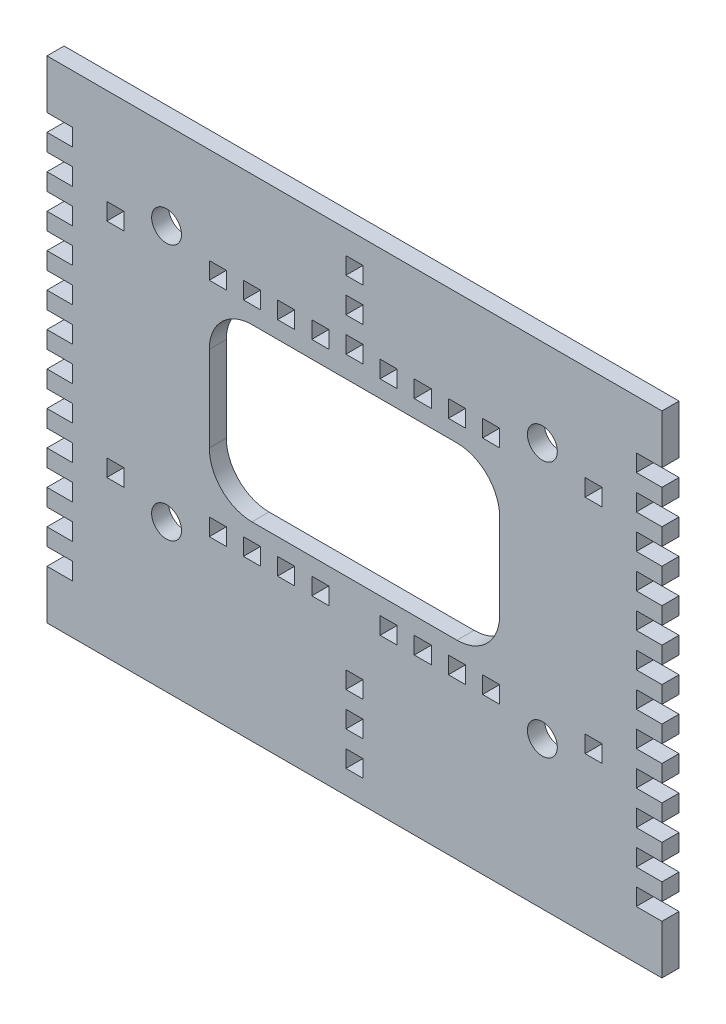
SolidWorks part; units mm, degrees
material "Cedar"
ref_plane "Front Plane" through (0, 0, 0) normal (0, 0, 1) x (1, 0, 0)
ref_plane "Top Plane" through (0, 0, 0) normal (0, 1, 0) x (1, 0, 0)
ref_plane "Right Plane" through (0, 0, 0) normal (1, 0, 0) x (0, 0, -1)
sketch "Sketch1" plane through (0, 0, 0) normal (0, 0, 1) x (1, 0, 0)
  line L0 (0, 0) -> (0, 50) construction
  line L1 (0, 0) -> (-60, 0) construction
  line L2 (-72, -57.5) -> (-72, 57.5)
  line L3 (-72, 57.5) -> (72, 57.5)
  line L6 (-2, 44) -> (2, 44)
  line L7 (72, -57.5) -> (72, 57.5)
  line L8 (-72, -57.5) -> (72, -57.5)
  line L9 (-24, 27) -> (24, 27)
  line L10 (-75.7581, 7) -> (88.9053, 7) construction
  line L11 (-34, 17) -> (-34, -3)
  line L12 (-24, -13) -> (24, -13)
  line L13 (34, 17) -> (34, -3)
  line L14 (-2, 52) -> (2, 52)
  line L15 (-2, 52) -> (-2, 48)
  line L16 (-2, 48) -> (2, 48)
  line L17 (2, 52) -> (2, 48)
  line L18 (-2, 44) -> (-2, 40)
  line L19 (-2, 40) -> (2, 40)
  line L20 (2, 44) -> (2, 40)
  line L21 (-2, 36) -> (2, 36)
  line L22 (-2, 36) -> (-2, 32)
  line L23 (-2, 32) -> (2, 32)
  line L24 (2, 36) -> (2, 32)
  line L25 (2, -36) -> (2, -32)
  line L26 (-2, -32) -> (2, -32)
  line L27 (-2, -36) -> (-2, -32)
  line L28 (-2, -36) -> (2, -36)
  line L29 (2, -44) -> (2, -40)
  line L30 (-2, -40) -> (2, -40)
  line L31 (-2, -44) -> (-2, -40)
  line L32 (2, -52) -> (2, -48)
  line L33 (-2, -48) -> (2, -48)
  line L34 (-2, -52) -> (-2, -48)
  line L35 (-2, -52) -> (2, -52)
  line L36 (-2, -44) -> (2, -44)
  circle A0 centre (-44, 37) radius 3.5
  arc A1 (-34, -3) -> (-24, -13) centre (-24, -3) ccw
  arc A2 (34, -3) -> (24, -13) centre (24, -3) cw
  circle A3 centre (44, 37) radius 3.5
  circle A4 centre (44, -23) radius 3.5
  circle A5 centre (-44, -23) radius 3.5
  arc A6 (34, 17) -> (24, 27) centre (24, 17) ccw
  arc A7 (-24, 27) -> (-34, 17) centre (-24, 17) ccw
  point P21 (0, 57.5)
  point P27 (-72, 0)
  point P28 (72, 0)
  dimension "D3" = 7
  dimension "D8" = 20
  dimension "D10" = 10
  dimension "D1" = 20.5
  dimension "D2" = 28
  dimension "D4" = 44
  dimension "D5" = 34
  dimension "D6" = 34
  dimension "D7" = 20
  dimension "D9" = 30
  dimension "D11" = 5.5
  dimension "D12" = 4
  dimension "D13" = 4
  dimension "D14" = 2
  dimension "D15" = 3
extrude "Boss-Extrude1" add sketch "Sketch1" along normal blind 4
sketch "Sketch2" plane through (0, 0, 4) normal (0, 0, 1) x (1, 0, 0)
  line L0 (0, 0) -> (-89.2695, 0) construction
  line L1 (0, 0) -> (0, 71.1996) construction
  line L2 (-72, -57.5) -> (-72, 57.5) construction
  line L3 (-72, 10) -> (-66, 10)
  line L4 (-72, 10) -> (-72, 14)
  line L5 (-72, 14) -> (-66, 14)
  line L6 (-66, 10) -> (-66, 14)
  line L8 (-72, 2) -> (-66, 2)
  line L9 (-72, 2) -> (-72, 6)
  line L10 (-72, 6) -> (-66, 6)
  line L11 (-66, 2) -> (-66, 6)
  line L12 (-72, 18) -> (-66, 18)
  line L13 (-72, 18) -> (-72, 22)
  line L14 (-72, 22) -> (-66, 22)
  line L15 (-66, 18) -> (-66, 22)
  line L16 (-72, 26) -> (-66, 26)
  line L17 (-72, 26) -> (-72, 30)
  line L18 (-72, 30) -> (-66, 30)
  line L19 (-66, 26) -> (-66, 30)
  line L20 (-72, 34) -> (-66, 34)
  line L21 (-72, 34) -> (-72, 38)
  line L22 (-72, 38) -> (-66, 38)
  line L23 (-66, 34) -> (-66, 38)
  line L24 (-72, 42) -> (-66, 42)
  line L25 (-72, 42) -> (-72, 46)
  line L26 (-72, 46) -> (-66, 46)
  line L27 (-66, 42) -> (-66, 46)
  line L28 (66, 42) -> (66, 46)
  line L29 (72, 46) -> (66, 46)
  line L30 (72, 42) -> (72, 46)
  line L31 (72, 42) -> (66, 42)
  line L32 (66, 34) -> (66, 38)
  line L33 (72, 38) -> (66, 38)
  line L34 (72, 34) -> (72, 38)
  line L35 (72, 34) -> (66, 34)
  line L36 (66, 26) -> (66, 30)
  line L37 (72, 30) -> (66, 30)
  line L38 (72, 26) -> (72, 30)
  line L39 (72, 26) -> (66, 26)
  line L40 (66, 18) -> (66, 22)
  line L41 (72, 22) -> (66, 22)
  line L42 (72, 18) -> (72, 22)
  line L43 (72, 18) -> (66, 18)
  line L44 (66, 2) -> (66, 6)
  line L45 (72, 6) -> (66, 6)
  line L46 (72, 2) -> (72, 6)
  line L47 (72, 2) -> (66, 2)
  line L48 (66, 10) -> (66, 14)
  line L49 (72, 14) -> (66, 14)
  line L50 (72, 10) -> (72, 14)
  line L51 (72, 10) -> (66, 10)
  line L52 (72, -10) -> (66, -10)
  line L53 (72, -10) -> (72, -14)
  line L54 (72, -14) -> (66, -14)
  line L55 (66, -10) -> (66, -14)
  line L56 (72, -2) -> (66, -2)
  line L57 (72, -2) -> (72, -6)
  line L58 (72, -6) -> (66, -6)
  line L59 (66, -2) -> (66, -6)
  line L60 (72, -18) -> (66, -18)
  line L61 (72, -18) -> (72, -22)
  line L62 (72, -22) -> (66, -22)
  line L63 (66, -18) -> (66, -22)
  line L64 (72, -26) -> (66, -26)
  line L65 (72, -26) -> (72, -30)
  line L66 (72, -30) -> (66, -30)
  line L67 (66, -26) -> (66, -30)
  line L68 (72, -34) -> (66, -34)
  line L69 (72, -34) -> (72, -38)
  line L70 (72, -38) -> (66, -38)
  line L71 (66, -34) -> (66, -38)
  line L72 (72, -42) -> (66, -42)
  line L73 (72, -42) -> (72, -46)
  line L74 (72, -46) -> (66, -46)
  line L75 (66, -42) -> (66, -46)
  line L76 (-66, -42) -> (-66, -46)
  line L77 (-72, -46) -> (-66, -46)
  line L78 (-72, -42) -> (-72, -46)
  line L79 (-72, -42) -> (-66, -42)
  line L80 (-66, -34) -> (-66, -38)
  line L81 (-72, -38) -> (-66, -38)
  line L82 (-72, -34) -> (-72, -38)
  line L83 (-72, -34) -> (-66, -34)
  line L84 (-66, -26) -> (-66, -30)
  line L85 (-72, -30) -> (-66, -30)
  line L86 (-72, -26) -> (-72, -30)
  line L87 (-72, -26) -> (-66, -26)
  line L88 (-66, -18) -> (-66, -22)
  line L89 (-72, -22) -> (-66, -22)
  line L90 (-72, -18) -> (-72, -22)
  line L91 (-72, -18) -> (-66, -18)
  line L92 (-66, -2) -> (-66, -6)
  line L93 (-72, -6) -> (-66, -6)
  line L94 (-72, -2) -> (-72, -6)
  line L95 (-72, -2) -> (-66, -2)
  line L96 (-66, -10) -> (-66, -14)
  line L97 (-72, -14) -> (-66, -14)
  line L98 (-72, -10) -> (-72, -14)
  line L99 (-72, -10) -> (-66, -10)
  dimension "D1" = 2
  dimension "D2" = 6
  dimension "D3" = 4
  dimension "D5" = 6
extrude "Cut-Extrude1" cut sketch "Sketch2" against normal blind 4
sketch "Sketch4" plane through (0, 0, 4) normal (0, 0, 1) x (1, 0, 0)
  line L0 (-24, -13) -> (24, -13) construction
  line L1 (6, -17) -> (10, -17)
  line L2 (6, -17) -> (6, -21)
  line L3 (6, -21) -> (10, -21)
  line L4 (10, -17) -> (10, -21)
  line L5 (0, 0) -> (0, 50) construction
  line L6 (14, -17) -> (18, -17)
  line L7 (14, -17) -> (14, -21)
  line L8 (14, -21) -> (18, -21)
  line L9 (18, -17) -> (18, -21)
  line L10 (22, -17) -> (26, -17)
  line L11 (22, -17) -> (22, -21)
  line L12 (22, -21) -> (26, -21)
  line L13 (26, -17) -> (26, -21)
  line L14 (30, -17) -> (34, -17)
  line L15 (30, -17) -> (30, -21)
  line L16 (30, -21) -> (34, -21)
  line L17 (34, -17) -> (34, -21)
  line L26 (54, -17) -> (58, -17)
  line L27 (54, -17) -> (54, -21)
  line L28 (54, -21) -> (58, -21)
  line L29 (58, -17) -> (58, -21)
  line L30 (0, 0) -> (0, -29.2897) construction
  line L31 (-58, -17) -> (-58, -21)
  line L32 (-54, -21) -> (-58, -21)
  line L33 (-54, -17) -> (-54, -21)
  line L34 (-54, -17) -> (-58, -17)
  line L43 (-34, -17) -> (-34, -21)
  line L44 (-30, -21) -> (-34, -21)
  line L45 (-30, -17) -> (-30, -21)
  line L46 (-30, -17) -> (-34, -17)
  line L47 (-26, -17) -> (-26, -21)
  line L48 (-22, -21) -> (-26, -21)
  line L49 (-22, -17) -> (-22, -21)
  line L50 (-22, -17) -> (-26, -17)
  line L51 (-18, -17) -> (-18, -21)
  line L52 (-14, -21) -> (-18, -21)
  line L53 (-14, -17) -> (-14, -21)
  line L54 (-14, -17) -> (-18, -17)
  line L55 (-10, -17) -> (-10, -21)
  line L56 (-6, -21) -> (-10, -21)
  line L57 (-6, -17) -> (-6, -21)
  line L58 (-6, -17) -> (-10, -17)
  line L59 (-24, 27) -> (24, 27) construction
  line L60 (6, 35) -> (10, 35)
  line L61 (6, 35) -> (6, 31)
  line L62 (6, 31) -> (10, 31)
  line L63 (10, 35) -> (10, 31)
  line L64 (14, 35) -> (18, 35)
  line L65 (14, 35) -> (14, 31)
  line L66 (14, 31) -> (18, 31)
  line L67 (18, 35) -> (18, 31)
  line L68 (22, 35) -> (26, 35)
  line L69 (22, 35) -> (22, 31)
  line L70 (22, 31) -> (26, 31)
  line L71 (26, 35) -> (26, 31)
  line L72 (30, 35) -> (34, 35)
  line L73 (30, 35) -> (30, 31)
  line L74 (30, 31) -> (34, 31)
  line L75 (34, 35) -> (34, 31)
  line L76 (-58, 35) -> (-58, 31)
  line L77 (-54, 31) -> (-58, 31)
  line L78 (-54, 35) -> (-54, 31)
  line L79 (-54, 35) -> (-58, 35)
  line L80 (-34, 35) -> (-34, 31)
  line L81 (-30, 31) -> (-34, 31)
  line L82 (-30, 35) -> (-30, 31)
  line L83 (-30, 35) -> (-34, 35)
  line L84 (54, 35) -> (58, 35)
  line L85 (54, 35) -> (54, 31)
  line L86 (54, 31) -> (58, 31)
  line L87 (58, 35) -> (58, 31)
  line L88 (38, 35) -> (42, 35) [skipped]
  line L89 (38, 35) -> (38, 31) [skipped]
  line L90 (38, 31) -> (42, 31) [skipped]
  line L91 (42, 35) -> (42, 31) [skipped]
  line L92 (46, 35) -> (50, 35) [skipped]
  line L93 (46, 35) -> (46, 31) [skipped]
  line L94 (46, 31) -> (50, 31) [skipped]
  line L95 (50, 35) -> (50, 31) [skipped]
  line L96 (-26, 35) -> (-26, 31)
  line L97 (-22, 31) -> (-26, 31)
  line L98 (-22, 35) -> (-22, 31)
  line L99 (-22, 35) -> (-26, 35)
  line L100 (-18, 35) -> (-18, 31)
  line L101 (-14, 31) -> (-18, 31)
  line L102 (-14, 35) -> (-14, 31)
  line L103 (-14, 35) -> (-18, 35)
  line L104 (-10, 35) -> (-10, 31)
  line L105 (-6, 31) -> (-10, 31)
  line L106 (-6, 35) -> (-6, 31)
  line L107 (-6, 35) -> (-10, 35)
  line L108 (38, -17) -> (42, -17) [skipped]
  line L109 (38, -17) -> (38, -21) [skipped]
  line L110 (38, -21) -> (42, -21) [skipped]
  line L111 (42, -17) -> (42, -21) [skipped]
  line L112 (46, -17) -> (50, -17) [skipped]
  line L113 (46, -17) -> (46, -21) [skipped]
  line L114 (46, -21) -> (50, -21) [skipped]
  line L115 (50, -17) -> (50, -21) [skipped]
  dimension "D1" = 4
  dimension "D2" = 4
  dimension "D3" = 4
  dimension "D4" = 6
  dimension "D6" = 4
  dimension "D7" = 4
  dimension "D8" = 4
  dimension "D9" = 6
  dimension "D5" = 7
  dimension "D10" = 7
extrude "Cut-Extrude2" cut sketch "Sketch4" against normal blind 10
